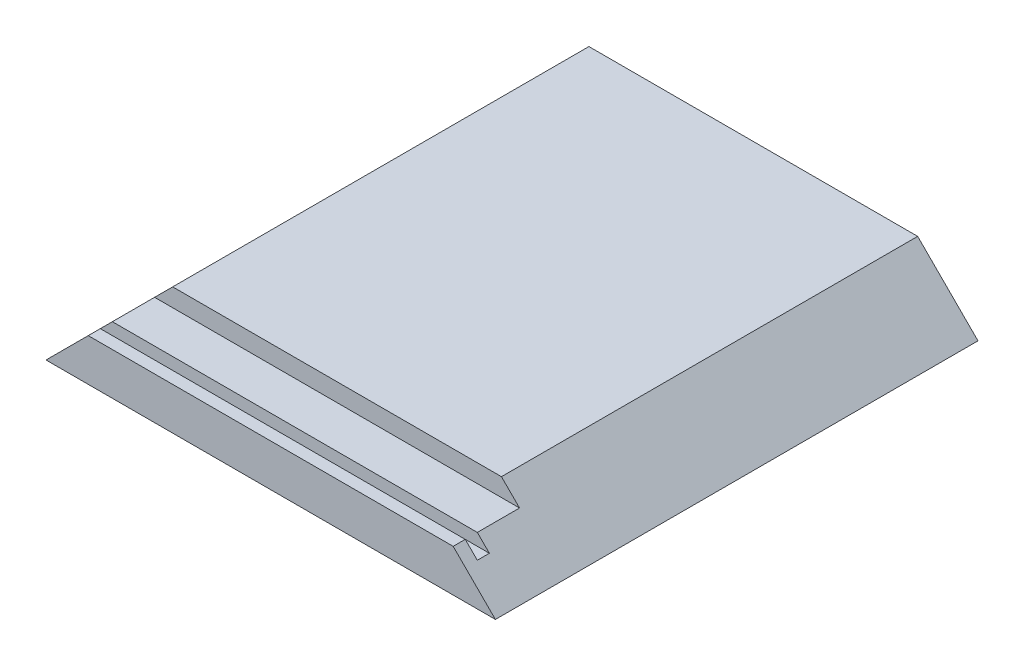
SolidWorks part; units mm, degrees
ref_plane "Front Plane" through (0, 0, 0) normal (0, 0, 1) x (1, 0, 0)
ref_plane "Top Plane" through (0, 0, 0) normal (0, 1, 0) x (1, 0, 0)
ref_plane "Right Plane" through (0, 0, 0) normal (1, 0, 0) x (0, 0, -1)
sketch "Sketch1" plane through (0, 0, 0) normal (0, 1, 0) x (1, 0, 0)
  line L1 (-37.25, 40) -> (37.25, 40)
  line L2 (-37.25, 40) -> (-37.25, -40)
  line L3 (-37.25, -40) -> (37.25, -40)
  line L4 (37.25, 40) -> (37.25, -40)
  line L5 (-37.25, 40) -> (37.25, -40) construction
  line L6 (-37.25, -40) -> (37.25, 40) construction
  point P0 (0, 0)
  dimension "D1" = 80
  dimension "D2" = 74.5
extrude "Boss-Extrude1" add sketch "Sketch1" along normal blind 10
sketch "Sketch2" plane through (-37.25, 0, 0) normal (-1, 0, 0) x (0, 0, 1)
  line L1 (40, 10) -> (29, 10)
  line L2 (40, 10) -> (40, 7)
  line L3 (40, 7) -> (29, 7)
  line L4 (29, 10) -> (29, 7)
  dimension "D1" = 3
  dimension "D2" = 11
extrude "Cut-Extrude1" cut sketch "Sketch2" against normal through all
sketch "Sketch3" plane through (-37.25, 0, 0) normal (-1, 0, 0) x (0, 0, 1)
  line L0 (29, 7) -> (40, 7) construction
  line L1 (38, 7) -> (36, 7)
  line L2 (38, 7) -> (38, 5)
  line L3 (38, 5) -> (36, 5)
  line L4 (36, 7) -> (36, 5)
  line L5 (40, 7) -> (40, 0) construction
  dimension "D1" = 2
  dimension "D2" = 2
  dimension "D3" = 2
extrude "Cut-Extrude2" cut sketch "Sketch3" against normal through all
sketch "Sketch4" plane through (0, 0, -40) normal (0, 0, -1) x (-1, 0, 0)
  line L0 (-37.25, 0) -> (-27.25, 10)
  line L2 (-27.25, 10) -> (-37.25, 10)
  line L3 (-37.25, 10) -> (-37.25, 0)
  line L4 (-37.25, 10) -> (37.25, 10) construction
  line L5 (37.25, 10) -> (37.25, 0)
  line L6 (0, 10) -> (0, 0) construction
  line L7 (-37.25, 0) -> (37.25, 0) construction
  line L8 (27.25, 10) -> (37.25, 10)
  line L9 (37.25, 0) -> (27.25, 10)
  dimension "D1" = 45
extrude "Cut-Extrude4" cut sketch "Sketch4" against normal through all
